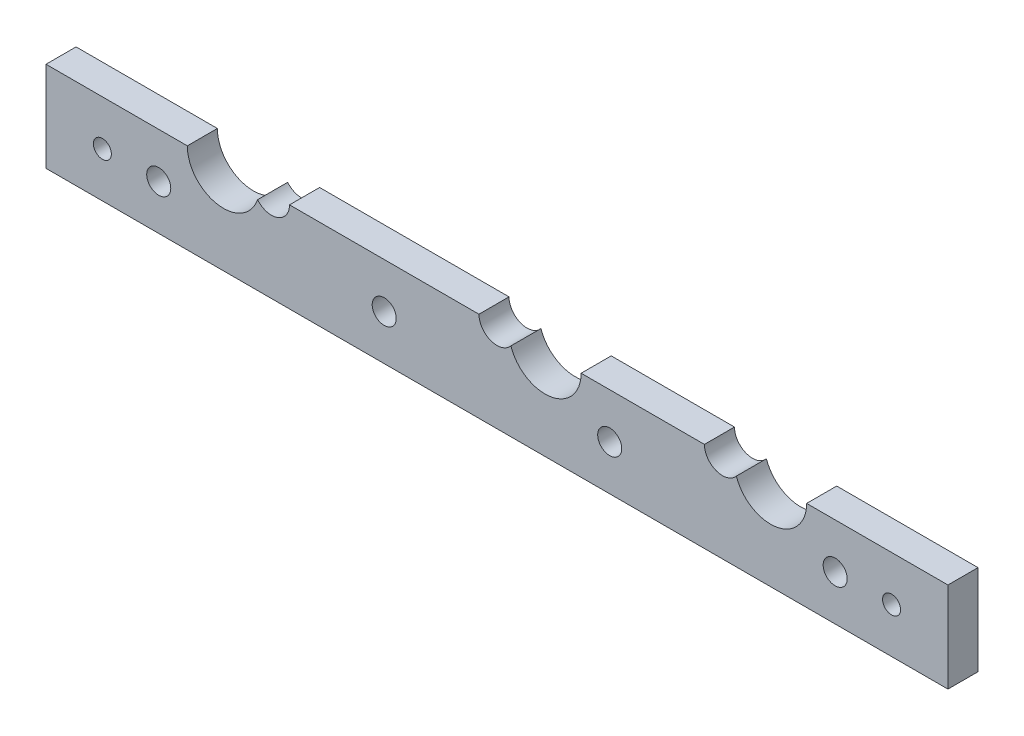
SolidWorks part; units mm, degrees
ref_plane "Front Plane" through (0, 0, 0) normal (0, 0, 1) x (1, 0, 0)
ref_plane "Top Plane" through (0, 0, 0) normal (0, 1, 0) x (1, 0, 0)
ref_plane "Right Plane" through (0, 0, 0) normal (1, 0, 0) x (0, 0, -1)
sketch "Sketch1" plane through (0, 0, 0) normal (0, 0, 1) x (1, 0, 0)
  line L1 (-56.8107, 18.5531) -> (93.1893, 18.5531)
  line L2 (-56.8107, 18.5531) -> (-56.8107, -11.4469)
  line L3 (-56.8107, -11.4469) -> (93.1893, -11.4469)
  line L4 (93.1893, 18.5531) -> (93.1893, -11.4469)
  dimension "D1" = 150
  dimension "D2" = 30
extrude "Boss-Extrude1" add sketch "Sketch1" along normal blind 5 contours L1 L4 L3 L2
sketch "Sketch2" plane through (0, 0, 5) normal (0, 0, 1) x (1, 0, 0)
  line L0 (55.6893, 3.5531) -> (55.6893, 18.5531) construction
  line L2 (93.1893, 18.5531) -> (93.1893, -11.4469) construction
  line L3 (18.1893, 18.5531) -> (18.1893, -11.4469) construction
  line L4 (-56.8107, 18.5531) -> (93.1893, 18.5531) construction
  line L5 (-56.8107, -11.4469) -> (93.1893, -11.4469) construction
  line L6 (18.1893, 3.5531) -> (93.1893, 3.5531) construction
sketch "Sketch3" plane through (0, 0, 0) normal (0, 1, 0) x (1, 0, 0)
  line L0 (18.1893, -5) -> (18.1893, -24.2528) construction
  line L1 (-56.8107, -5) -> (93.1893, -5) construction
ref_plane "Plane1" through (18.1893, 0, 0) normal (-1, 0, 0) x (0, 0, 1)
hole_wizard "Ø6.0mm Dowel Hole1" positions "3DSketch2" profile "Sketch4" hole size "Ø6.0" standard "ISO"
sketch3d "3DSketch2"
  point P0 (55.6893, 3.5531, 5)
  point P3 (18.1893, 3.5531, 5)
sketch "Sketch4" plane through (55.6893, 3.5531, 5) normal (1, 0, 0) x (0, -1, 0)
  line L0 (0, 0) -> (0, 26.8026)
  line L1 (0, 26.8026) -> (3, 25)
  line L2 (3, 25) -> (3, 0)
  line L5 (3, 0) -> (0, 0)
  line L10 (0, 26.8026) -> (-3, 25) construction
  line L11 (0, -6.35) -> (0, 107.95) construction
  dimension "Hole Dia." = 6
  dimension "Hole Depth" = 25
  dimension "Drill Angle" = 118
mirror "Mirror1" about plane through (18.1893, 0, 0) normal (-1, 0, 0) of "Ø6.0mm Dowel Hole1"
sketch "Sketch5" plane through (0, 0, 5) normal (0, 0, 1) x (1, 0, 0)
  line L0 (93.1893, 3.5531) -> (93.1893, 18.5531) construction
  line L1 (93.1893, 18.5531) -> (93.1893, -11.4469) construction
  line L2 (55.6893, 11.0531) -> (18.1893, 11.0531) construction
  line L4 (36.9393, 11.0531) -> (36.9393, 18.5531) construction
  line L5 (55.6893, 11.0531) -> (93.1893, 11.0531) construction
  line L6 (-56.8107, 18.5531) -> (93.1893, 18.5531) construction
  line L7 (74.4393, 11.0531) -> (74.4393, 18.5531) construction
hole_wizard "Ø4.0mm Dowel Hole1" positions "3DSketch3" profile "Sketch6" hole size "Ø4.0" standard "ISO"
sketch3d "3DSketch3"
  point P0 (74.4393, 11.0531, 5)
  point P3 (36.9393, 11.0531, 5)
sketch "Sketch6" plane through (74.4393, 11.0531, 5) normal (1, 0, 0) x (0, -1, 0)
  line L0 (0, 0) -> (0, 26.2017)
  line L1 (0, 26.2017) -> (2, 25)
  line L2 (2, 25) -> (2, 0)
  line L5 (2, 0) -> (0, 0)
  line L10 (0, 26.2017) -> (-2, 25) construction
  line L11 (0, -6.35) -> (0, 107.95) construction
  dimension "Hole Dia." = 4
  dimension "Hole Depth" = 25
  dimension "Drill Angle" = 118
sketch "Sketch7" plane through (0, 0, 0) normal (1, 0, 0) x (0, 0, -1)
  line L0 (-5, 3.5531) -> (-23.0008, 3.5531) construction
  line L1 (-5, 18.5531) -> (-5, -11.4469) construction
ref_plane "Plane2" through (0, 3.5531, 0) normal (0, 1, 0) x (1, 0, 0)
mirror "Mirror2" about plane through (0, 3.5531, 0) normal (0, 1, 0) of "Ø4.0mm Dowel Hole1"
mirror "Mirror3" about plane through (18.1893, 0, 0) normal (-1, 0, 0) of "Mirror2", "Ø4.0mm Dowel Hole1"
sketch "Sketch8" plane through (0, 0, 5) normal (0, 0, 1) x (1, 0, 0)
  line L0 (50.1893, 3.5531) -> (61.1893, 3.5531) construction
  line L1 (55.6893, 3.5531) -> (55.6893, 18.5531) construction
  line L2 (36.9393, 18.5531) -> (36.9393, 3.5531) construction
  line L3 (23.6893, 3.5531) -> (12.6893, 3.5531) construction
  dimension "D1" = 5.5
sketch "Sketch16" plane through (0, 0, 0) normal (0, 0, -1) x (-1, 0, 0)
  line L0 (-50.1893, 13.5531) -> (-49.1893, 13.5531)
  line L1 (-49.1893, 13.5531) -> (-49.1893, 11.5531)
  line L2 (-49.1893, 11.5531) -> (-50.1893, 11.5531)
  line L3 (-50.1893, 11.5531) -> (-50.1893, 13.5531)
sketch "Sketch17" plane through (0, 0, 0) normal (0, 0, -1) x (-1, 0, 0)
  line L0 (-55.6893, 0.5531) -> (-55.6893, -11.4469) construction
  line L1 (-23.6893, -11.4469) -> (-93.1893, -11.4469) construction
  arc A0 (-58.6893, 3.5531) -> (-52.6893, 3.5531) centre (-55.6893, 3.5531) ccw construction
sketch "Sketch18" plane through (0, -11.4469, 0) normal (0, -1, 0) x (1, 0, 0)
  line L0 (55.6893, 0) -> (55.6893, 4.6302) construction
ref_plane "Plane3" through (55.6893, 0, 0) normal (-1, 0, 0) x (0, 0, 1)
sketch "Sketch19" plane through (0, 0, 0) normal (0, 0, -1) x (-1, 0, 0)
  line L0 (-18.1893, 6.5531) -> (-18.1893, 18.5531) construction
  line L1 (13.8107, 18.5531) -> (-50.1893, 18.5531) construction
  arc A0 (-15.1893, 3.5531) -> (-21.1893, 3.5531) centre (-18.1893, 3.5531) ccw construction
sketch "Sketch20" plane through (0, 18.5531, 0) normal (0, 1, 0) x (1, 0, 0)
  line L0 (18.1893, 0) -> (18.1893, -5) construction
  line L1 (-13.8107, 0) -> (50.1893, 0) construction
  line L2 (-13.8107, -5) -> (50.1893, -5) construction
ref_plane "Plane4" through (18.1893, 0, 0) normal (1, 0, 0) x (0, 0, -1)
sketch "Sketch22" plane through (0, 0, 5) normal (0, 0, 1) x (1, 0, 0)
  line L0 (-38.0607, -3.9469) -> (-56.8107, -3.9469) construction
  line L1 (-56.8107, 18.5531) -> (-56.8107, -11.4469) construction
  line L2 (-47.4357, -3.9469) -> (-47.4357, -11.4469) construction
  line L3 (-56.8107, -11.4469) -> (93.1893, -11.4469) construction
hole_wizard "Ø3.0mm Dowel Hole2" positions "3DSketch5" profile "Sketch23" hole size "Ø3.0" standard "ISO"
sketch3d "3DSketch5"
  point P0 (-47.4357, -3.9469, 5)
sketch "Sketch23" plane through (-47.4357, -3.9469, 5) normal (1, 0, 0) x (0, -1, 0)
  line L0 (0, 0) -> (0, 25.9013)
  line L1 (0, 25.9013) -> (1.5, 25)
  line L2 (1.5, 25) -> (1.5, 0)
  line L5 (1.5, 0) -> (0, 0)
  line L10 (0, 25.9013) -> (-1.5, 25) construction
  line L11 (0, -6.35) -> (0, 107.95) construction
  dimension "Hole Dia." = 3
  dimension "Hole Depth" = 25
  dimension "Drill Angle" = 118
mirror "Mirror5" about plane through (18.1893, 0, 0) normal (-1, 0, 0) of "Ø3.0mm Dowel Hole2"
sketch "Sketch27" plane through (0, 0, 5) normal (0, 0, 1) x (1, 0, 0)
  line L0 (21.1893, 3.5531) -> (26.1893, 3.5531) construction
  circle A0 centre (18.1893, 3.5531) radius 3 construction
  dimension "D1" = 5
hole_wizard "Ø12.0mm Dowel Hole2" positions "3DSketch11" profile "Sketch29" hole size "Ø12.0" standard "ISO"
sketch3d "3DSketch11"
  point P0 (26.1893, 3.5531, 5)
sketch "Sketch29" plane through (26.1893, 3.5531, 5) normal (1, 0, 0) x (0, -1, 0)
  line L0 (0, 0) -> (0, 28.6052)
  line L1 (0, 28.6052) -> (6, 25)
  line L2 (6, 25) -> (6, 0)
  line L5 (6, 0) -> (0, 0)
  line L10 (0, 28.6052) -> (-6, 25) construction
  line L11 (0, -6.35) -> (0, 107.95) construction
  dimension "Hole Dia." = 12
  dimension "Hole Depth" = 25
  dimension "Drill Angle" = 118
sketch "Sketch30" plane through (0, 0, 5) normal (0, 0, 1) x (1, 0, 0)
  line L0 (-56.8107, 18.5531) -> (-56.8107, -11.4469) construction
  line L1 (93.1893, 18.5531) -> (-56.8107, 18.5531)
  line L2 (93.1893, 18.5531) -> (93.1893, 3.5531)
  line L3 (93.1893, 3.5531) -> (-56.8107, 3.5531)
  line L4 (-56.8107, 18.5531) -> (-56.8107, 3.5531)
  line L5 (26.1893, -2.4469) -> (26.1893, 3.5531) construction
  line L6 (26.1893, 3.5531) -> (18.1893, 3.5531) construction
  line L7 (55.6893, 3.5531) -> (64.3373, 3.5531) construction
  arc A0 (20.5018, 1.6419) -> (20.5018, 5.4642) centre (26.1893, 3.5531) ccw construction
extrude "Cut-Extrude1" cut sketch "Sketch30" against normal blind 10 contours L3 L4 L1 L2
sketch "Sketch31" plane through (0, 0, 5) normal (0, 0, 1) x (1, 0, 0)
  line L0 (55.6893, 3.5531) -> (63.6893, 3.5531) construction
  line L1 (93.1893, 3.5531) -> (58.6893, 3.5531) construction
  line L2 (-19.3107, 3.5531) -> (-27.3107, 3.5531) construction
  line L3 (-22.3107, 3.5531) -> (-56.8107, 3.5531) construction
  dimension "D1" = 8
  dimension "D2" = 8
hole_wizard "Ø12.0mm Dowel Hole3" positions "Sketch35" profile "Sketch32" hole size "Ø12.0" standard "ISO"
sketch "Sketch35" plane through (0, 0, 5) normal (0, 0, 1) x (1, 0, 0)
  point P0 (63.6893, 3.5531)
  point P3 (-27.3107, 3.5531)
sketch "Sketch32" plane through (63.6893, 3.5531, 5) normal (1, 0, 0) x (0, -1, 0)
  line L0 (0, 0) -> (0, 16.3552)
  line L1 (0, 16.3552) -> (6, 12.75)
  line L2 (6, 12.75) -> (6, 0)
  line L5 (6, 0) -> (0, 0)
  line L10 (0, 16.3552) -> (-6, 12.75) construction
  line L11 (0, -6.35) -> (0, 107.95) construction
  dimension "Hole Dia." = 12
  dimension "Hole Depth" = 12.75
  dimension "Drill Angle" = 118
